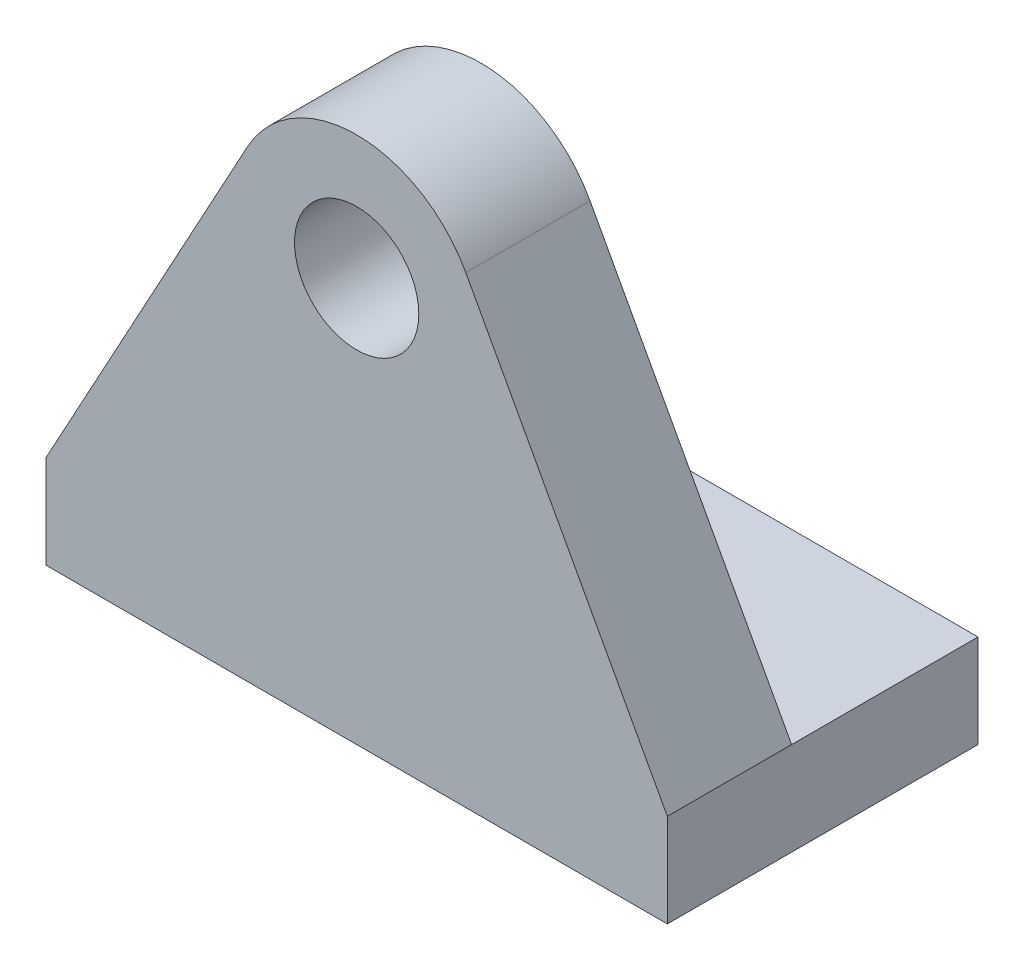
SolidWorks part; units mm, degrees
ref_plane "前视基准面" through (0, 0, 0) normal (0, 0, 1) x (1, 0, 0)
ref_plane "上视基准面" through (0, 0, 0) normal (0, 1, 0) x (1, 0, 0)
ref_plane "右视基准面" through (0, 0, 0) normal (1, 0, 0) x (0, 0, -1)
sketch "草图1" plane through (0, 0, 0) normal (0, 0, 1) x (1, 0, 0)
  line L1 (-10, -10) -> (10, -10)
  line L2 (10, -10) -> (3.5129, 1.9129)
  line L3 (-10, -10) -> (-3.5129, 1.9129)
  circle A0 centre (0, 0) radius 2
  arc A1 (3.5129, 1.9129) -> (-3.5129, 1.9129) centre (0, 0) ccw
  dimension "D1" = 4
  dimension "D2" = 8
extrude "凸台-拉伸1" add sketch "草图1" along normal blind 4
sketch "草图2" plane through (0, 0, 4) normal (0, 0, 1) x (1, 0, 0)
  line L1 (-10, -10) -> (10, -10)
  line L2 (-10, -10) -> (-10, -13)
  line L3 (-10, -13) -> (10, -13)
  line L4 (10, -10) -> (10, -13)
  dimension "D1" = 3
extrude "凸台-拉伸2" add sketch "草图2" against normal blind 10
